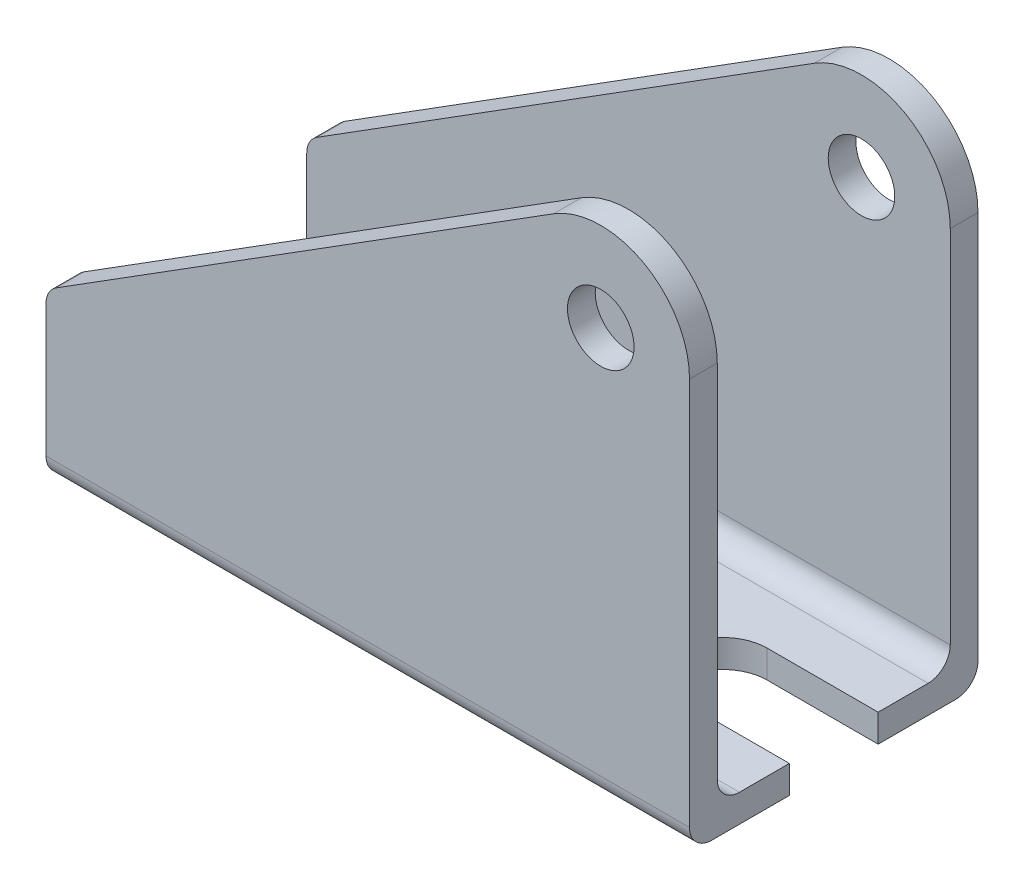
SolidWorks part; units mm, degrees
ref_plane "Front Plane" through (0, 0, 0) normal (0, 0, 1) x (1, 0, 0)
ref_plane "Top Plane" through (0, 0, 0) normal (0, 1, 0) x (1, 0, 0)
ref_plane "Right Plane" through (0, 0, 0) normal (1, 0, 0) x (0, 0, -1)
sketch "Sketch1" plane through (0, 0, 0) normal (0, 0, 1) x (1, 0, 0)
  line L0 (-20.6252, -9.7803) -> (37.3748, -9.7803)
  line L1 (37.3748, -9.7803) -> (37.3748, 27.2197)
  line L2 (25.1153, 33.9914) -> (-20.6252, 5.2197)
  line L3 (-20.6252, 5.2197) -> (-20.6252, -9.7803)
  arc A0 (25.1153, 33.9914) -> (37.3748, 27.2197) centre (29.3748, 27.2197) cw
  circle A1 centre (29.3748, 27.2197) radius 3
  dimension "D1" = 8
  dimension "D3" = 6
  dimension "D5" = 37
  dimension "D2" = 58
  dimension "D4" = 15
extrude "Boss-Extrude1" add sketch "Sketch1" along normal blind 26
shell "Shell1" thickness 2.5
fillet "Fillet1" radius 2 6 edges at (8.3748, -9.7803, 26) (8.3748, -9.7803, 0) (-20.6252, 5.2197, 24.75) (-20.6252, 5.2197, 1.25) (8.3748, -7.2803, 23.5) (8.3748, -7.2803, 2.5)
sketch "Sketch2" plane through (0, 0, 0) normal (0, 1, 0) x (1, 0, 0)
  line L0 (-20.6252, -21.5) -> (-20.6252, -4.5) construction
  circle A0 centre (-8.6252, -13) radius 4
  dimension "D1" = 8
  dimension "D2" = 12
  dimension "D3" = 13
extrude "Cut-Extrude1" cut sketch "Sketch2" against normal through all
sketch "Sketch3" plane through (0, 0, 0) normal (0, 1, 0) x (1, 0, 0)
  line L0 (37.3748, -9) -> (27.3748, -9)
  line L1 (37.3748, -21.5) -> (37.3748, -4.5) construction
  line L3 (27.3748, -17) -> (37.3748, -17)
  line L4 (37.3748, -17) -> (37.3748, -9)
  line L5 (-20.6252, -21.5) -> (-20.6252, -4.5) construction
  arc A0 (27.3748, -9) -> (27.3748, -17) centre (27.3748, -13) ccw
  dimension "D1" = 4
  dimension "D2" = 48
  dimension "D3" = 9
extrude "Cut-Extrude2" cut sketch "Sketch3" against normal through all
